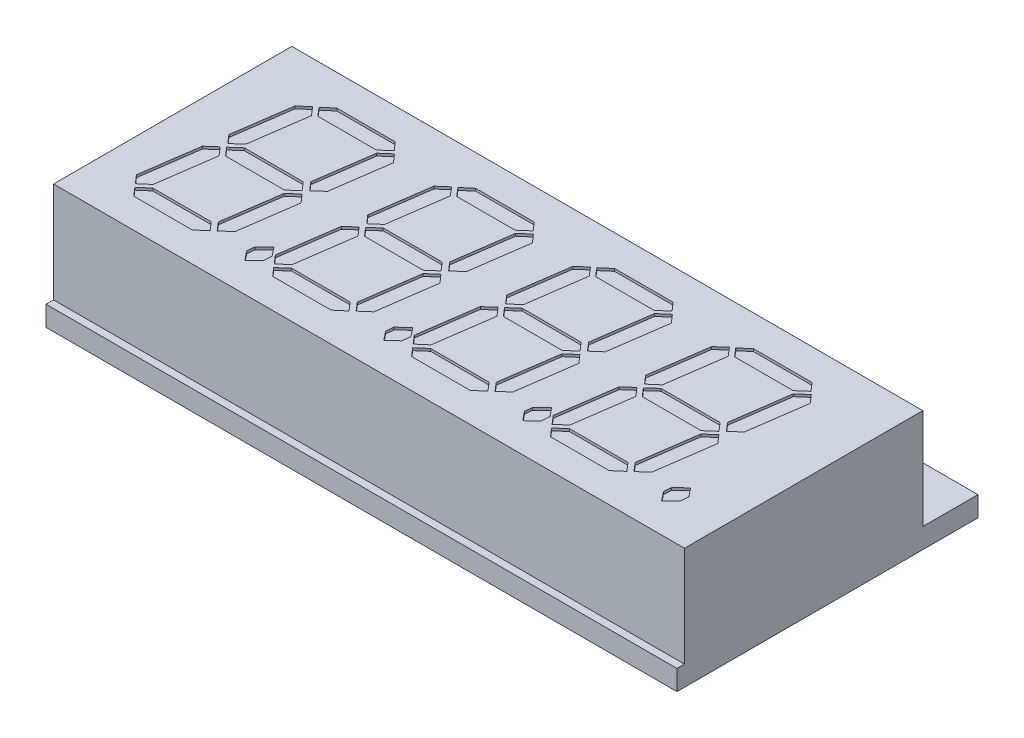
SolidWorks part; units mm, degrees
ref_plane "Front Plane" through (0, 0, 0) normal (0, 0, 1) x (1, 0, 0)
ref_plane "Top Plane" through (0, 0, 0) normal (0, 1, 0) x (1, 0, 0)
ref_plane "Right Plane" through (0, 0, 0) normal (1, 0, 0) x (0, 0, -1)
sketch "Sketch1" plane through (0, 0, 0) normal (0, 1, 0) x (1, 0, 0)
  line L1 (0, 0) -> (50.3, 0)
  line L2 (0, 0) -> (0, 19)
  line L3 (0, 19) -> (50.3, 19)
  line L4 (50.3, 0) -> (50.3, 19)
  dimension "D1" = 19
  dimension "D2" = 50.3
extrude "Boss-Extrude1" add sketch "Sketch1" along normal blind 8
sketch "Sketch3" plane through (0, 0, 0) normal (0, -1, 0) x (1, 0, 0)
  line L1 (0, 0.6) -> (50.3, 0.6)
  line L2 (0, 0.6) -> (0, -23.4)
  line L3 (0, -23.4) -> (50.3, -23.4)
  line L4 (50.3, 0.6) -> (50.3, -23.4)
  dimension "D1" = 0.6
  dimension "D2" = 4.4
  dimension "D3" = 50.3
extrude "Boss-Extrude2" add sketch "Sketch3" along normal blind 1.6
sketch "Sketch4" plane through (0, -1.6, 0) normal (0, -1, 0) x (1, 0, 0)
  line L0 (-0.4922, -10.5894) -> (15.9466, -10.5894) construction
  line L1 (2.5, -4.4) -> (13, -4.4)
  line L2 (2.5, -4.4) -> (2.5, -10.4)
  line L3 (2.5, -10.4) -> (13, -10.4)
  line L4 (13, -4.4) -> (13, -10.4)
  line L6 (13, -16.7788) -> (13, -10.7788)
  line L7 (2.5, -10.7788) -> (13, -10.7788)
  line L8 (2.5, -16.7788) -> (2.5, -10.7788)
  line L9 (2.5, -16.7788) -> (13, -16.7788)
  dimension "D1" = 2.5
  dimension "D2" = 5
  dimension "D3" = 6
  dimension "D4" = 10.5
extrude "Boss-Extrude3" [suppressed] add sketch "Sketch4" along normal blind 2
sketch "Sketch5" [suppressed] plane through (0, -3.6, 0) normal (0, -1, 0) x (1, 0, 0)
  line L0 (2.5, -10.4) -> (13, -10.4)
  line L1 (13, -10.4) -> (13, -9.4)
  line L2 (13, -10.4) -> (13, -4.4) construction
  line L3 (13, -9.4) -> (9, -9.4)
  line L4 (9, -9.4) -> (9, -10)
  line L5 (9, -10) -> (6.5, -10)
  line L6 (6.5, -10) -> (6.5, -9.4)
  line L7 (6.5, -9.4) -> (2.5, -9.4)
  line L8 (2.5, -4.4) -> (2.5, -10.4) construction
  line L9 (2.5, -9.4) -> (2.5, -10.4)
  line L10 (7.75, -4.4) -> (7.75, -10.4) construction
  line L11 (13, -4.4) -> (2.5, -4.4) construction
  line L12 (2.5, -7.4) -> (13, -7.4) construction
  line L13 (7.75, -4.4) -> (2.5, -10.4) construction
  line L14 (2.5, -4.4) -> (7.75, -10.4) construction
  line L15 (5.125, -7.4) -> (5.125, -4.4) construction
  line L16 (13, -4.4) -> (2.5, -4.4) construction
  line L17 (5.125, -4.4) -> (5.125, -10.4) construction
  line L18 (5.125, -4.4) -> (2.5, -10.4) construction
  line L19 (5.125, -4.4) -> (7.75, -10.4) construction
  line L20 (13, -10.4) -> (13, -10.7788) construction
  line L21 (13, -10.5894) -> (0, -10.5894) construction
  line L22 (0, 0.6) -> (0, -23.4) construction
  line L23 (2.5, -16.78) -> (13, -16.78)
  line L24 (13, -16.78) -> (13, -15.78)
  line L25 (13, -15.78) -> (9, -15.78)
  line L26 (9, -15.78) -> (9, -16.38)
  line L27 (9, -16.38) -> (6.5, -16.38)
  line L28 (6.5, -16.38) -> (6.5, -15.78)
  line L29 (6.5, -15.78) -> (2.5, -15.78)
  line L30 (2.5, -15.78) -> (2.5, -16.78)
  circle A0 centre (3.8125, -7.4) radius 0.2
  circle A1 centre (6.4375, -7.4) radius 0.2
  circle A2 centre (11.6875, -7.4) radius 0.2
  circle A3 centre (9.0625, -7.4) radius 0.2
  circle A4 centre (3.8125, -13.78) radius 0.2
  circle A5 centre (6.4375, -13.78) radius 0.2
  circle A6 centre (11.6875, -13.78) radius 0.2
  circle A7 centre (9.0625, -13.78) radius 0.2
  dimension "D4" = 2
  dimension "D1" = 2.5
  dimension "D2" = 1
  dimension "D3" = 0.4
extrude "Boss-Extrude4" [suppressed] add sketch "Sketch5" along normal blind 5
fillet "Fillet1" [suppressed] radius 0.1
sketch "Sketch6" plane through (0, 8, 0) normal (0, 1, 0) x (1, 0, 0)
  text T0 "8.8.8.8." font "LCDMono2" height in points 48
extrude "Cut-Extrude1" cut sketch "Sketch6" against normal blind 0.2
